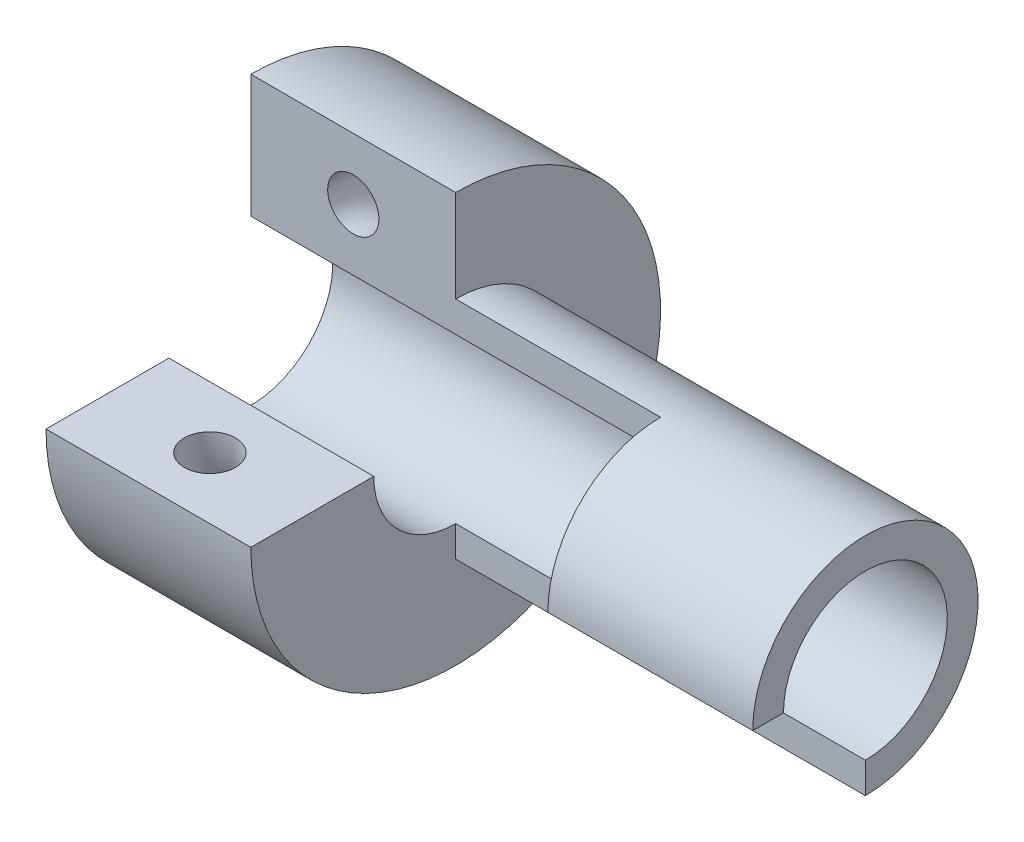
SolidWorks part; units mm, degrees
ref_plane "Front Plane" through (0, 0, 0) normal (0, 0, 1) x (1, 0, 0)
ref_plane "Top Plane" through (0, 0, 0) normal (0, 1, 0) x (1, 0, 0)
ref_plane "Right Plane" through (0, 0, 0) normal (1, 0, 0) x (0, 0, -1)
sketch "Sketch1" plane through (0, 0, 0) normal (0, 1, 0) x (1, 0, 0)
  line L0 (0, 0) -> (20, 0)
  line L1 (20, 0) -> (20, 12)
  line L2 (20, 12) -> (0, 12)
  line L3 (0, 12) -> (0, 0)
  line L4 (0, 12) -> (0, 20)
  line L5 (0, 20) -> (20, 20)
  line L6 (20, 20) -> (20, 12)
  dimension "D1" = 20
  dimension "D2" = 12
  dimension "D3" = 8
revolve "Revolve2" add sketch "Sketch1" angle 270 about L5
sketch "Sketch4" plane through (0, 0, 0) normal (0, 1, 0) x (1, 0, 0)
  circle A0 centre (10, 6) radius 2.5
  dimension "D2" = 5
  dimension "D1" = 10
  dimension "D3" = 6
sketch "Sketch5" plane through (0, 0, 0) normal (-1, 0, 0) x (0, 0, 1)
  line L0 (-12, 0) -> (-20, 0)
  line L1 (-20, 0) -> (-20, 8)
  line L2 (-20, 8) -> (-12, 0)
sketch "Sketch6" plane through (20, 0, 0) normal (1, 0, 0) x (0, 0, -1)
  line L0 (12, 0) -> (20, 0)
  line L1 (20, 0) -> (20, 8)
  line L2 (20, 8) -> (12, 0)
sketch "Sketch7" plane through (0, 0, 0) normal (0, 1, 0) x (1, 0, 0)
  line L0 (20, 20) -> (0, 20)
  line L1 (20, 12) -> (20, 20) construction
  line L2 (0, 12) -> (0, 20) construction
revolve "Cut-Revolve1" cut sketch "Sketch4" angle 270 about L0
sketch "Sketch9" plane through (20, 0, 0) normal (1, 0, 0) x (0, 0, -1)
  line L0 (20, 20) -> (20, 8) construction
  line L1 (20, -11) -> (20, -8)
  line L2 (20, 8) -> (20, 11)
  arc A0 (20, 11) -> (20, -11) centre (20, 0) cw
  arc A1 (20, 8) -> (20, -8) centre (20, 0) cw
  dimension "D1" = 11
extrude "Boss-Extrude3" add sketch "Sketch9" along normal blind 40
sketch "Sketch10" plane through (0, 0, -20) normal (0, 0, 1) x (1, 0, 0)
  line L0 (40, 11) -> (40, 8)
  line L1 (60, 11) -> (20, 11) construction
  line L2 (60, 8) -> (0, 8) construction
  line L3 (40, 8) -> (60, 8)
  line L4 (60, 8) -> (60, 11)
  line L5 (60, 11) -> (40, 11)
  dimension "D1" = 20
revolve "Revolve4" add sketch "Sketch10" angle 90 about L0
